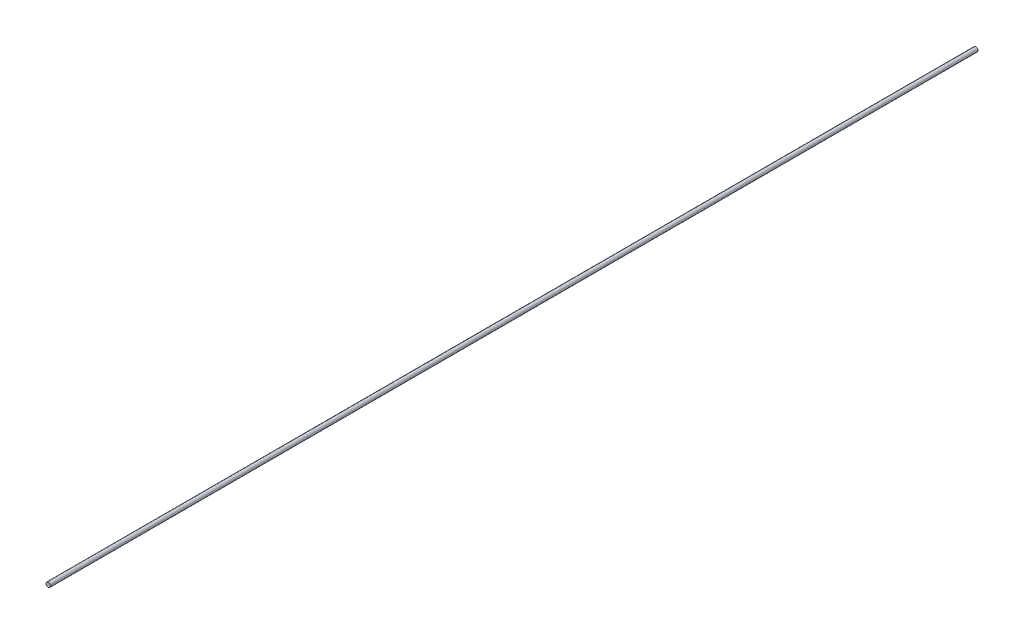
SolidWorks part; units mm, degrees
ref_plane "Front Plane" through (0, 0, 0) normal (0, 0, 1) x (1, 0, 0)
ref_plane "Top Plane" through (0, 0, 0) normal (0, 1, 0) x (1, 0, 0)
ref_plane "Right Plane" through (0, 0, 0) normal (1, 0, 0) x (0, 0, -1)
sketch "Sketch1" plane through (0, 0, 0) normal (0, 0, 1) x (1, 0, 0)
  circle A0 centre (0, 0) radius 3.8
  dimension "D1" = 7.6
extrude "Boss-Extrude1" add sketch "Sketch1" along normal blind 1586
